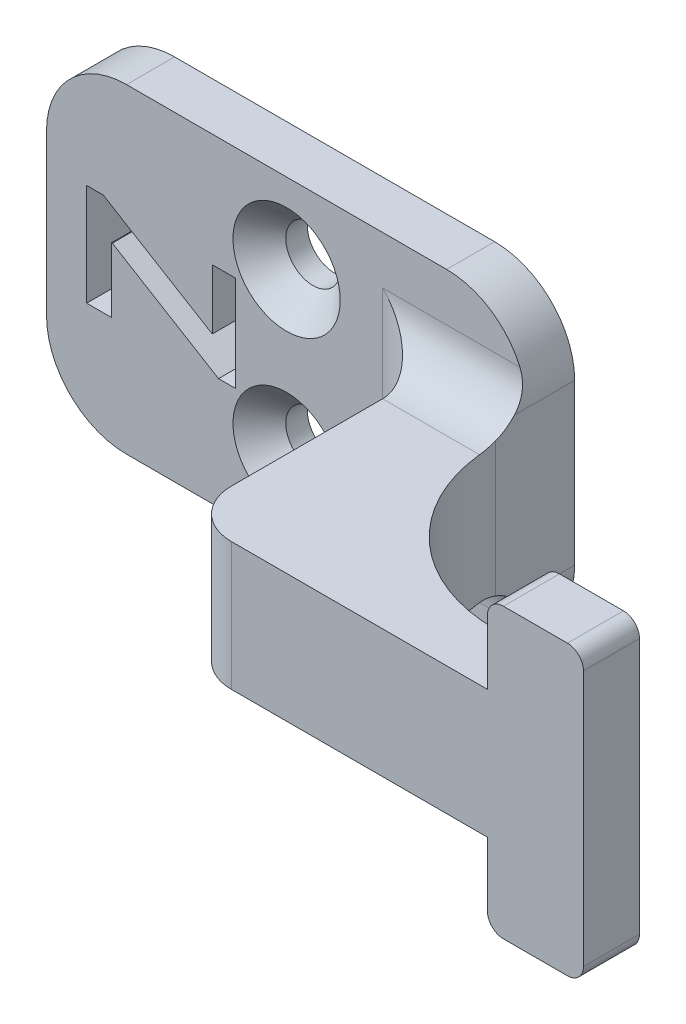
SolidWorks part; units mm, degrees
ref_plane "Front Plane" through (0, 0, 0) normal (0, 0, 1) x (1, 0, 0)
ref_plane "Top Plane" through (0, 0, 0) normal (0, 1, 0) x (1, 0, 0)
ref_plane "Right Plane" through (0, 0, 0) normal (1, 0, 0) x (0, 0, -1)
sketch "Sketch1" plane through (0, 0, 0) normal (0, 0, 1) x (1, 0, 0)
  line L1 (-10, -10) -> (10, -10)
  line L2 (-15, -5) -> (-15, 5)
  line L3 (-10, 10) -> (10, 10)
  line L4 (15, -5) -> (15, 5)
  line L5 (-15, -10) -> (15, 10) construction
  line L6 (-15, 10) -> (15, -10) construction
  arc A0 (-15, -5) -> (-10, -10) centre (-10, -5) ccw
  arc A1 (10, -10) -> (15, -5) centre (10, -5) ccw
  arc A2 (15, 5) -> (10, 10) centre (10, 5) ccw
  arc A3 (-10, 10) -> (-15, 5) centre (-10, 5) ccw
  point P0 (0, 0)
  dimension "D3" = 5
  dimension "D1" = 20
  dimension "D2" = 30
extrude "Boss-Extrude1" add sketch "Sketch1" along normal blind 3
sketch "Sketch2" plane through (0, 0, 0) normal (0, 1, 0) x (1, 0, 0)
  line L0 (0, 0) -> (15, 0) construction
  line L1 (15, 0) -> (15, -14.95)
  line L2 (15, 0) -> (9, 0)
  line L3 (9, 0) -> (9, -18.45)
  line L4 (9, -18.45) -> (34, -18.45)
  line L5 (34, -18.45) -> (34, -14.95)
  line L6 (34, -14.95) -> (15, -14.95)
  line L7 (34, -16.7) -> (9, -16.7) construction
  dimension "D1" = 6
  dimension "D2" = 3.5
  dimension "D3" = 16.7
  dimension "D4" = 25
extrude "Boss-Extrude2" add sketch "Sketch2" along normal mid plane 8
sketch "Sketch3" plane through (0, 0, 18.45) normal (0, 0, 1) x (1, 0, 0)
  line L1 (34, 4) -> (28, 4)
  line L2 (34, 4) -> (34, 9)
  line L3 (34, 9) -> (28, 9)
  line L4 (28, 4) -> (28, 9)
  line L5 (34, -4) -> (28, -4)
  line L6 (34, -4) -> (34, -9)
  line L7 (34, -9) -> (28, -9)
  line L8 (28, -4) -> (28, -9)
  dimension "D1" = 6
  dimension "D2" = 5
  dimension "D3" = 6
  dimension "D4" = 5
extrude "Boss-Extrude3" add sketch "Sketch3" against normal up to surface (3.5 mm away) up to face at (24.5, 0, 14.95)
fillet "Fillet1" radius 3 4 edges at (12, 4, 3) (9, 0, 3) (12, -4, 3) (9, 0, 18.45)
fillet "Fillet3" radius 10 1 edges at (15, 0, 14.95)
sketch "Sketch4" plane through (0, 0, 3) normal (0, 0, 1) x (1, 0, 0)
  line L0 (0, -5) -> (0, 5) construction
  point P4 (0, 5)
  point P6 (0, 0)
  point P8 (0, -5)
  dimension "D1" = 10
hole_wizard "CSK for M3 Countersunk Flat Head Screw1" positions "3DSketch1" profile "Sketch5" countersink size "M3" standard "DIN"
sketch3d "3DSketch1"
  point P0 (0, 5, 3)
  point P3 (0, -5, 3)
sketch "Sketch5" plane through (0, 5, 3) normal (1, 0, 0) x (0, -1, 0)
  line L0 (0, 0) -> (0, 21.0215)
  line L1 (0, 21.0215) -> (1.7, 20)
  line L2 (1.7, 20) -> (1.7, 1.65)
  line L3 (1.7, 1.65) -> (3.35, 0)
  line L5 (3.35, 0) -> (0, 0)
  line L6 (-1.7, 1.65) -> (-3.35, 0) construction
  line L10 (0, 21.0215) -> (-1.7, 20) construction
  line L11 (0, -6.35) -> (0, 107.95) construction
  dimension "Hole Dia." = 3.4
  dimension "Hole Depth" = 20
  dimension "Near C'Sink Dia." = 6.7
  dimension "Near C'Sink Angle" = 90
  dimension "Drill Angle" = 118
sketch "Sketch6" plane through (0, 0, 3) normal (0, 0, 1) x (1, 0, 0)
  line L0 (-12.5, 10) -> (-12.5, -10) construction
  line L1 (-15, 5) -> (-15, -5) construction
  text T0 "Z" font "@Adobe Gothic Std B" height in points 30
  dimension "D1" = 2.5
extrude "Cut-Extrude1" cut sketch "Sketch6" against normal blind 10
fillet "Fillet4" radius 1 4 edges at (28, 9, 16.7) (34, 9, 16.7) (34, -9, 16.7) (28, -9, 16.7)
